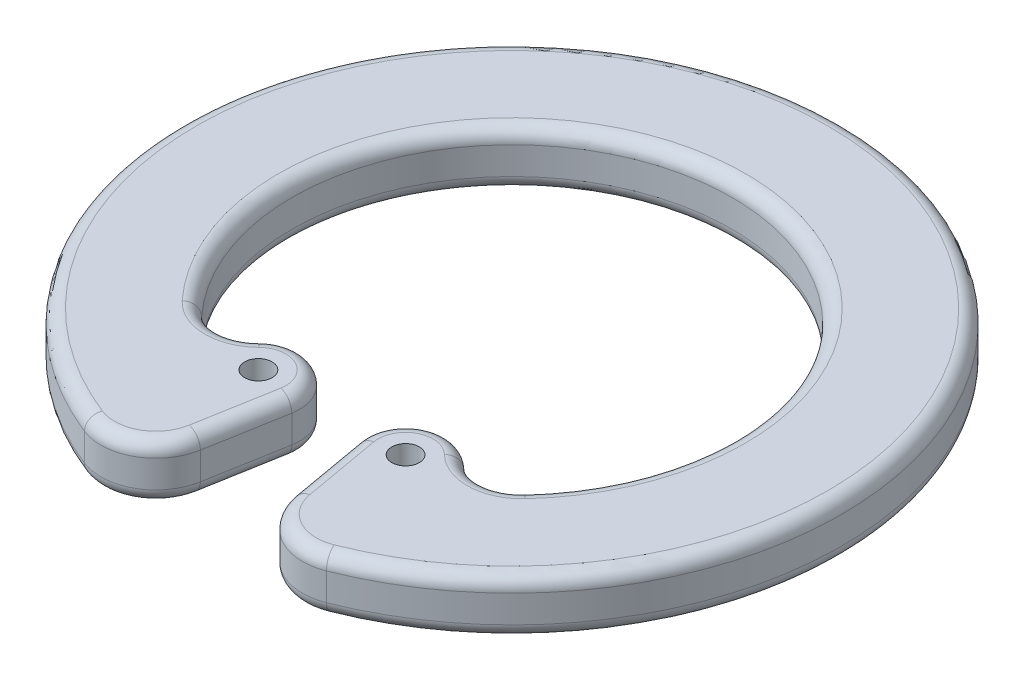
SolidWorks part; units mm, degrees
ref_plane "Front Plane" through (0, 0, 0) normal (0, 0, 1) x (1, 0, 0)
ref_plane "Top Plane" through (0, 0, 0) normal (0, 1, 0) x (1, 0, 0)
ref_plane "Right Plane" through (0, 0, 0) normal (1, 0, 0) x (0, 0, -1)
sketch "Sketch1" plane through (0, 0, 0) normal (0, 1, 0) x (1, 0, 0)
  line L0 (0, 0) -> (0, -12) construction
  line L1 (1.7014, -9.6491) -> (1.2021, -6.8177)
  line L2 (-1.7014, -9.6491) -> (-1.2021, -6.8177)
  arc A0 (5.8767, -5.4281) -> (-5.8767, -5.4281) centre (0, 0) ccw
  arc A1 (4.4052, -11.1622) -> (-4.4052, -11.1622) centre (0, 0) ccw
  arc A2 (1.2021, -6.8177) -> (3.7271, -5.4838) centre (2.6794, -6.5572) cw
  arc A3 (3.7271, -5.4838) -> (5.8767, -5.4281) centre (4.7748, -4.4103) ccw
  arc A4 (1.7014, -9.6491) -> (4.4052, -11.1622) centre (3.671, -9.3018) ccw
  circle A5 centre (2.6794, -6.5572) radius 0.5
  circle A6 centre (-2.6794, -6.5572) radius 0.5
  arc A7 (-3.7271, -5.4838) -> (-5.8767, -5.4281) centre (-4.7748, -4.4103) cw
  arc A8 (-1.7014, -9.6491) -> (-4.4052, -11.1622) centre (-3.671, -9.3018) cw
  arc A9 (-1.2021, -6.8177) -> (-3.7271, -5.4838) centre (-2.6794, -6.5572) ccw
  point P13 (2.0838, -11.8177)
  dimension "D1" = 16
  dimension "D2" = 24
  dimension "D5" = 1.5
  dimension "D6" = 1.5
  dimension "D7" = 2
  dimension "D8" = 1
  dimension "D3" = 5
  dimension "D4" = 10
extrude "Boss-Extrude1" add sketch "Sketch1" along normal mid plane 2
fillet "Fillet1" radius 0.5 20 edges at (2.6943, -1, 11.0471) (1.4518, -1, 8.2334) (1.9787, -1, 5.2309) (4.8136, -1, 5.9098) (0, -1, -8) (-4.8136, -1, 5.9098) (-1.9787, -1, 5.2309) (-1.4518, -1, 8.2334) (-2.6943, -1, 11.0471) (2.6943, 1, 11.0471) (1.4518, 1, 8.2334) (1.9787, 1, 5.2309) (4.8136, 1, 5.9098) (0, 1, -8) (-4.8136, 1, 5.9098) (-1.9787, 1, 5.2309) (-1.4518, 1, 8.2334) (-2.6943, 1, 11.0471) (0, -1, -12) (0, 1, -12)
